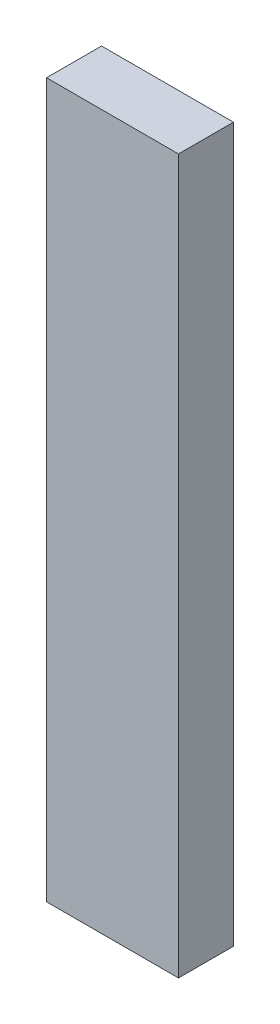
SolidWorks part; units mm, degrees
ref_plane "Front Plane" through (0, 0, 0) normal (0, 0, 1) x (1, 0, 0)
ref_plane "Top Plane" through (0, 0, 0) normal (0, 1, 0) x (1, 0, 0)
ref_plane "Right Plane" through (0, 0, 0) normal (1, 0, 0) x (0, 0, -1)
sketch "Sketch2" plane through (0, 0, 0) normal (0, 1, 0) x (1, 0, 0)
  line L0 (-39.7297, 70.3116) -> (-27.7297, 70.3116) construction
  line L1 (-39.7297, 75.3116) -> (-39.7297, 70.3116) construction
  line L2 (-27.7297, 70.3116) -> (-27.7297, 75.3116) construction
  line L3 (-39.7297, 70.3116) -> (-27.7297, 70.3116)
  line L4 (-39.7297, 75.3116) -> (-39.7297, 70.3116)
  line L5 (-27.7297, 70.3116) -> (-27.7297, 75.3116)
  line L7 (-27.7297, 70.3116) -> (-39.7297, 70.3116)
  line L8 (-27.7297, 70.3116) -> (-27.7297, 75.3116)
  line L9 (-27.7297, 75.3116) -> (-39.7297, 75.3116)
  line L10 (-39.7297, 70.3116) -> (-39.7297, 75.3116)
extrude "Boss-Extrude1" add sketch "Sketch2" along normal blind 15 contours L5 L9 L4 L3
sketch "Sketch3" plane through (0, 0, 0) normal (0, -1, 0) x (1, 0, 0)
  line L1 (-27.7297, -75.3116) -> (-39.7297, -75.3116)
  line L2 (-27.7297, -75.3116) -> (-27.7297, -70.3116)
  line L3 (-27.7297, -70.3116) -> (-39.7297, -70.3116)
  line L4 (-39.7297, -75.3116) -> (-39.7297, -70.3116)
extrude "Boss-Extrude2" add sketch "Sketch3" along normal up to surface (57.0016 mm away)
sketch "Sketch4" plane through (0, -57.0016, 0) normal (0, -1, 0) x (1, 0, 0)
  line L1 (-27.7297, -75.3116) -> (-39.7297, -75.3116)
  line L2 (-27.7297, -75.3116) -> (-27.7297, -70.3116)
  line L3 (-27.7297, -70.3116) -> (-39.7297, -70.3116)
  line L4 (-39.7297, -75.3116) -> (-39.7297, -70.3116)
extrude "Cut-Extrude1" cut sketch "Sketch4" against normal blind 7.1
